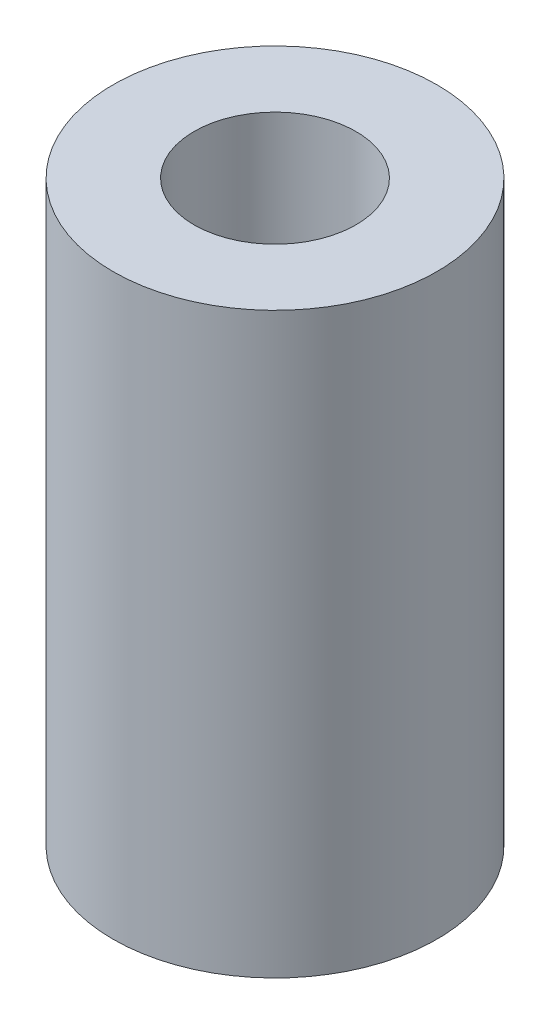
SolidWorks part; units mm, degrees
ref_plane "Alzado" through (0, 0, 0) normal (0, 0, 1) x (1, 0, 0)
ref_plane "Planta" through (0, 0, 0) normal (0, 1, 0) x (1, 0, 0)
ref_plane "Vista lateral" through (0, 0, 0) normal (1, 0, 0) x (0, 0, -1)
sketch "Croquis1" plane through (0, 0, 0) normal (0, 1, 0) x (1, 0, 0)
  circle A0 centre (0, 0) radius 3.5
  circle A1 centre (0, 0) radius 7
  dimension "D1" = 14
  dimension "D2" = 7
extrude "Saliente-Extruir1" add sketch "Croquis1" along normal blind 25 contours A1 A0
